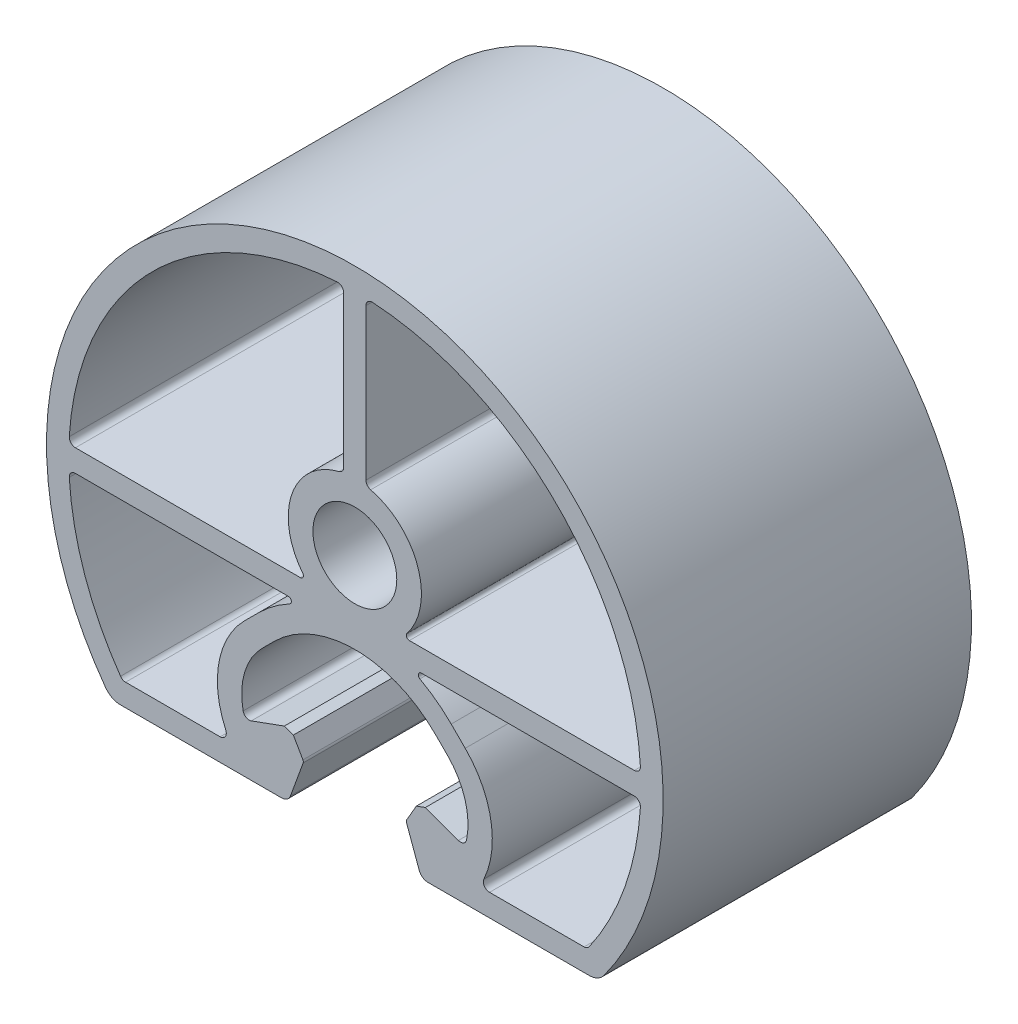
SolidWorks part; units mm, degrees
material "6005-T5"
ref_plane "Front" through (0, 0, 0) normal (0, 0, 1) x (1, 0, 0)
ref_plane "Top" through (0, 0, 0) normal (0, 1, 0) x (1, 0, 0)
ref_plane "Right" through (0, 0, 0) normal (1, 0, 0) x (0, 0, -1)
sketch "Sk Main Extrusion" plane through (0, 0, 0) normal (0, 0, 1) x (1, 0, 0)
  line L26 (4.419, 0.9) -> (22.6568, 0.9)
  line L27 (0.9, 22.6568) -> (0.9, 10.4022)
  line L28 (-22.6568, 0.9) -> (-4.419, 0.9)
  line L29 (-0.9, 10.4022) -> (-0.9, 22.6568)
  line L30 (-18.5884, -13.5293) -> (-10.9225, -13.5293)
  line L31 (5.9268, -15.3293) -> (19, -15.3293)
  line L32 (-19, -15.3293) -> (-5.9268, -15.3293)
  line L33 (-5.2221, -14.8358) -> (-4.1901, -12.0005)
  line L34 (-4.2085, -11.79) -> (-4.9876, -10.4406)
  line L35 (-4.9876, -10.4406) -> (-5.7185, -10.1746)
  line L36 (-5.7185, -10.1746) -> (-8.3962, -11.1492)
  line L37 (-7.5042, -5.602) -> (-6.5407, -4.6386)
  line L38 (6.5407, -4.6386) -> (7.5042, -5.602)
  line L39 (8.3962, -11.1492) -> (5.7185, -10.1746)
  line L40 (5.7185, -10.1746) -> (4.9876, -10.4406)
  line L41 (4.9876, -10.4406) -> (4.2085, -11.79)
  line L42 (4.1901, -12.0005) -> (5.2221, -14.8358)
  line L43 (-8.9493, -4.4016) -> (-7.8135, -3.2658)
  line L44 (-5.3943, -0.9) -> (-22.6568, -0.9)
  line L45 (7.8135, -3.2658) -> (8.9493, -4.4016)
  line L46 (10.9225, -13.5293) -> (18.5884, -13.5293)
  line L47 (22.6568, -0.9) -> (5.3943, -0.9)
  circle A39 centre (0, 4.6707) radius 3.4
  arc A40 (4.2234, 1.3058) -> (4.419, 0.9) centre (4.419, 1.15) ccw
  arc A41 (22.6568, 0.9) -> (23.1558, 1.4308) centre (22.6568, 1.4) ccw
  arc A42 (23.1558, 1.4308) -> (1.4308, 23.1558) centre (0, 0) ccw
  arc A43 (1.4308, 23.1558) -> (0.9, 22.6568) centre (1.4, 22.6568) ccw
  arc A44 (5.2221, -14.8358) -> (5.9268, -15.3293) centre (5.9268, -14.5793) ccw
  arc A45 (19, -15.3293) -> (20.2128, -14.712) centre (19, -13.8293) ccw
  arc A46 (20.2128, -14.712) -> (-20.2128, -14.712) centre (0, 0) ccw
  arc A47 (-20.2128, -14.712) -> (-19, -15.3293) centre (-19, -13.8293) ccw
  arc A48 (-5.9268, -15.3293) -> (-5.2221, -14.8358) centre (-5.9268, -14.5793) ccw
  arc A49 (-4.1901, -12.0005) -> (-4.2085, -11.79) centre (-4.425, -11.915) ccw
  arc A50 (-9.057, -10.78) -> (-8.3962, -11.1492) centre (-8.5672, -10.6793) ccw
  arc A51 (-7.5042, -5.602) -> (-9.057, -10.78) centre (-3.4737, -9.6325) ccw
  arc A52 (6.5407, -4.6386) -> (-6.5407, -4.6386) centre (0, -11.1793) ccw
  arc A53 (9.057, -10.78) -> (7.5042, -5.602) centre (3.4737, -9.6325) ccw
  arc A54 (8.3962, -11.1492) -> (9.057, -10.78) centre (8.5672, -10.6793) ccw
  arc A55 (4.2085, -11.79) -> (4.1901, -12.0005) centre (4.425, -11.915) ccw
  arc A56 (0.9, 10.4022) -> (1.2814, 9.9165) centre (1.4, 10.4022) ccw
  arc A57 (4.2234, 1.3058) -> (1.2814, 9.9165) centre (0, 4.6707) ccw
  arc A58 (-23.1558, 1.4308) -> (-22.6568, 0.9) centre (-22.6568, 1.4) ccw
  arc A59 (-4.419, 0.9) -> (-4.2234, 1.3058) centre (-4.419, 1.15) ccw
  arc A60 (-1.2814, 9.9165) -> (-4.2234, 1.3058) centre (0, 4.6707) ccw
  arc A61 (-1.2814, 9.9165) -> (-0.9, 10.4022) centre (-1.4, 10.4022) ccw
  arc A62 (-0.9, 22.6568) -> (-1.4308, 23.1558) centre (-1.4, 22.6568) ccw
  arc A63 (-1.4308, 23.1558) -> (-23.1558, 1.4308) centre (0, 0) ccw
  arc A64 (-22.6568, -0.9) -> (-23.1558, -1.4308) centre (-22.6568, -1.4) ccw
  arc A65 (-23.1558, -1.4308) -> (-18.9978, -13.3163) centre (0, 0) ccw
  arc A66 (-18.9978, -13.3163) -> (-18.5884, -13.5293) centre (-18.5884, -13.0293) ccw
  arc A67 (-10.9225, -13.5293) -> (-10.4678, -12.8215) centre (-10.9225, -13.0293) ccw
  arc A68 (-8.9493, -4.4016) -> (-10.4678, -12.8215) centre (-3.646, -9.7049) ccw
  arc A69 (-5.275, -1.3697) -> (-7.8135, -3.2658) centre (0, -11.0793) ccw
  arc A70 (-5.275, -1.3697) -> (-5.3943, -0.9) centre (-5.3943, -1.15) ccw
  arc A71 (5.3943, -0.9) -> (5.275, -1.3697) centre (5.3943, -1.15) ccw
  arc A72 (7.8135, -3.2658) -> (5.275, -1.3697) centre (0, -11.0793) ccw
  arc A73 (10.4678, -12.8215) -> (8.9493, -4.4016) centre (3.646, -9.7049) ccw
  arc A74 (10.4678, -12.8215) -> (10.9225, -13.5293) centre (10.9225, -13.0293) ccw
  arc A75 (18.5884, -13.5293) -> (18.9978, -13.3163) centre (18.5884, -13.0293) ccw
  arc A76 (18.9978, -13.3163) -> (23.1558, -1.4308) centre (0, 0) ccw
  arc A77 (23.1558, -1.4308) -> (22.6568, -0.9) centre (22.6568, -1.4) ccw
  point P86 (0, 0)
extrude "Main Extrusion" add sketch "Sk Main Extrusion" against normal blind 25
sketch "Threaded Insert Mate Sketch" plane through (0, 0, 0) normal (0, 0, 1) x (1, 0, 0)
  line L1 (5.9268, -15.3293) -> (19, -15.3293) construction
  circle A0 centre (0, -8.0293) radius 5.6515
  dimension "D2" = 11.303
  dimension "D1" = 7.3
equation "\"Weight kg\"= round ( \"SW-Mass\" , 2 )"
equation "\"Weight lbs\"= round ( \"SW-Mass\" * 2.2046 , 2 )"
equation "\"Length mm\"= round ( \"Length@Main Extrusion\" , 2 )"
equation "\"Length in\"= round ( \"Length@Main Extrusion\" / 25.4 , 3 )"
